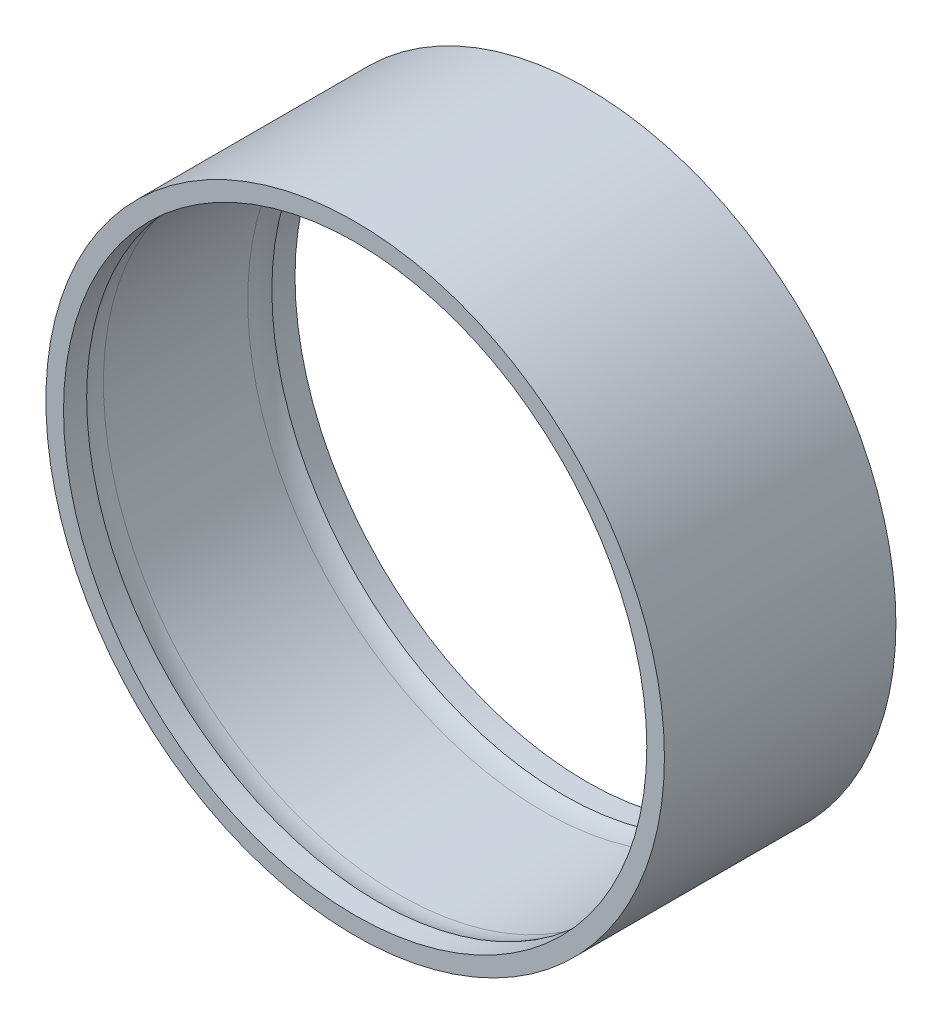
SolidWorks part; units mm, degrees
material "Plain Carbon Steel"
ref_plane "Front Plane" through (0, 0, 0) normal (0, 0, 1) x (1, 0, 0)
ref_plane "Top Plane" through (0, 0, 0) normal (0, 1, 0) x (1, 0, 0)
ref_plane "Right Plane" through (0, 0, 0) normal (1, 0, 0) x (0, 0, -1)
sketch "Sketch1" plane through (0, 0, 0) normal (0, 0, 1) x (1, 0, 0)
  circle A0 centre (0, 0) radius 42.418
  circle A1 centre (0, 0) radius 40
  circle A2 centre (0, 0) radius 44.45 construction
  circle A3 centre (0, 0) radius 39.6875 construction
  circle A4 centre (0, 0) radius 42.5 construction
  dimension "D1" = 84.836
  dimension "D2" = 80
  dimension "D3" = 88.9
  dimension "D4" = 4.7625
  dimension "D5" = 85
extrude "Extrude1" add sketch "Sketch1" along normal mid plane 31.75
sketch "Sketch2" plane through (0, 0, 0) normal (1, 0, 0) x (0, 0, -1)
  line L0 (-15.875, 40) -> (15.875, 40) construction
  line L1 (-9.8927, 40.513) -> (9.8927, 40.513)
  line L2 (15.875, 42.418) -> (-15.875, 42.418) construction
  line L3 (-15.875, 40) -> (-12.7, 40)
  line L4 (15.875, 40) -> (12.7, 40)
  line L5 (-15.875, 0) -> (15.875, 0) construction
  line L6 (-15.875, 42.418) -> (-15.875, -42.418) construction
  line L7 (15.875, -42.418) -> (15.875, 42.418) construction
  line L8 (-15.875, 40) -> (-15.875, 0)
  line L9 (-15.875, 0) -> (15.875, 0)
  line L10 (0, 40.513) -> (0, 0) construction
  line L11 (15.875, 40) -> (15.875, 0)
  arc A0 (-9.8927, 40.513) -> (-12.7, 40) centre (-9.8927, 32.5755) ccw
  arc A1 (9.8927, 40.513) -> (12.7, 40) centre (9.8927, 32.5755) cw
  dimension "D3" = 7.9375
  dimension "D1" = 1.905
  dimension "D2" = 3.175
revolve "Cut-Revolve1" cut sketch "Sketch2" angle 360 about L9
